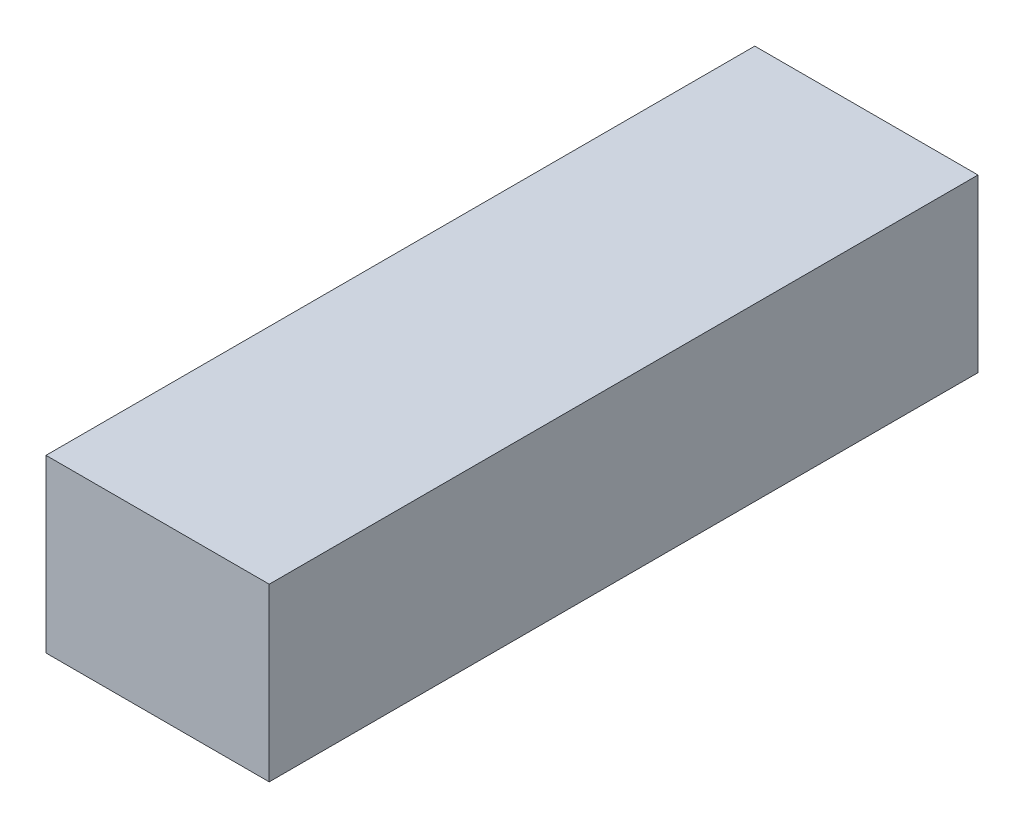
SolidWorks part; units mm, degrees
ref_plane "Front Plane" through (0, 0, 0) normal (0, 0, 1) x (1, 0, 0)
ref_plane "Top Plane" through (0, 0, 0) normal (0, 1, 0) x (1, 0, 0)
ref_plane "Right Plane" through (0, 0, 0) normal (1, 0, 0) x (0, 0, -1)
sketch "Sketch1" plane through (0, 0, 0) normal (0, 0, 1) x (1, 0, 0)
  line L1 (-24.25, -18.6) -> (24.25, -18.6)
  line L2 (-24.25, -18.6) -> (-24.25, 18.6)
  line L3 (-24.25, 18.6) -> (24.25, 18.6)
  line L4 (24.25, -18.6) -> (24.25, 18.6)
  line L5 (-24.25, -18.6) -> (24.25, 18.6) construction
  line L6 (-24.25, 18.6) -> (24.25, -18.6) construction
  point P0 (0, 0)
  dimension "D1" = 48.5
  dimension "D2" = 37.2
extrude "Boss-Extrude1" add sketch "Sketch1" along normal blind 154
sketch "Sketch2" plane through (0, 0, 154) normal (0, 0, 1) x (1, 0, 0)
  circle A0 centre (0, 0) radius 30.5618
